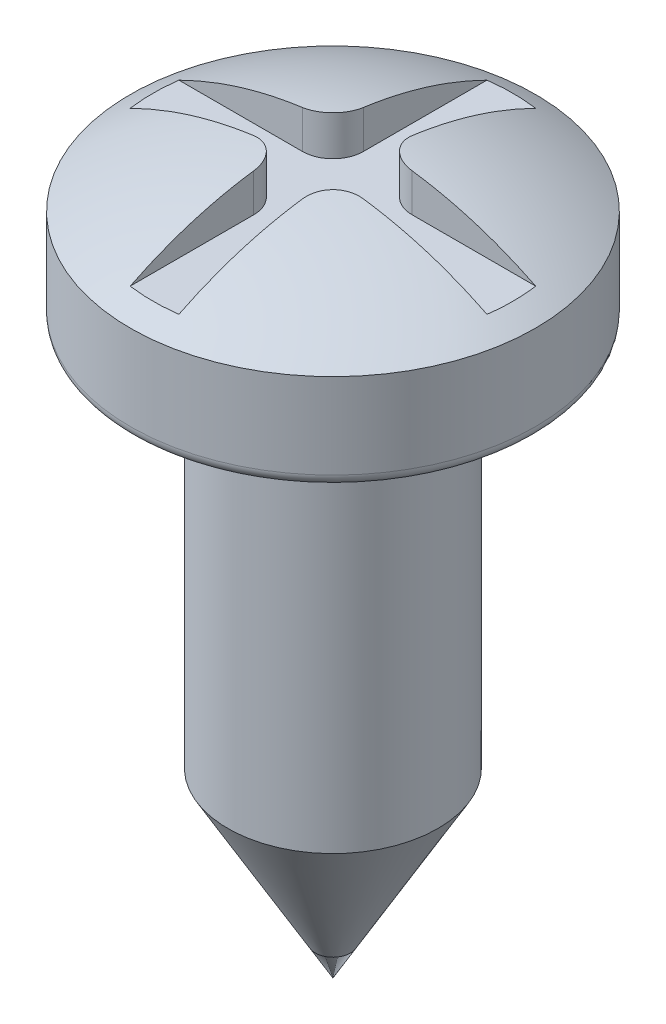
SolidWorks part; units mm, degrees
material "acero"
ref_plane "Alzado" through (0, 0, 0) normal (0, 0, 1) x (1, 0, 0)
ref_plane "Planta" through (0, 0, 0) normal (0, 1, 0) x (1, 0, 0)
ref_plane "Vista lateral" through (0, 0, 0) normal (1, 0, 0) x (0, 0, -1)
sketch "Croquis1" plane through (0, 0, 0) normal (0, 0, 1) x (1, 0, 0)
  line L0 (0, 0) -> (0, 11.8) construction
  line L1 (0, 0) -> (0, 11.8)
  line L2 (3.325, 9.5) -> (3.325, 10.9)
  line L3 (3.125, 9.3) -> (1.725, 9.3)
  line L4 (1.725, 9.3) -> (1.725, 2.9878)
  line L5 (1.725, 2.9878) -> (0, 0)
  line L6 (0, 11.8) -> (0, 14.3369) construction
  line L7 (0, 11.8) -> (-1.1321, 11.8) construction
  arc A0 (3.125, 9.3) -> (3.325, 9.5) centre (3.125, 9.5) ccw
  arc A1 (3.325, 10.9) -> (0, 11.8) centre (0, 5.208) ccw
  point P11 (3.325, 9.3)
  dimension "D7" = 0.2
  dimension "D1" = 1.6
  dimension "D2" = 30
  dimension "D3" = 2.5
  dimension "D4" = 3.45
  dimension "D5" = 6.65
  dimension "D9" = 9.3
revolve "Revolución1" add sketch "Croquis1" angle 360 about L0
sketch "Croquis2" plane through (0, 9.3, 0) normal (0, -1, 0) x (1, 0, 0)
  line L0 (0, 0) -> (0, 3.325) construction
  line L1 (-0.4, 3.2) -> (-0.4, 0.9)
  line L2 (-0.9, 0.4) -> (-3.2, 0.4)
  line L3 (-3.2, 0.4) -> (-3.2, -0.4)
  line L4 (-3.2, -0.4) -> (-0.9, -0.4)
  line L5 (-0.4, -0.9) -> (-0.4, -3.2)
  line L6 (-0.4, -3.2) -> (0.4, -3.2)
  line L7 (0.4, -3.2) -> (0.4, -0.9)
  line L8 (0.9, -0.4) -> (3.2, -0.4)
  line L9 (3.2, -0.4) -> (3.2, 0.4)
  line L10 (3.2, 0.4) -> (0.9, 0.4)
  line L11 (0.4, 0.9) -> (0.4, 3.2)
  line L12 (0.4, 3.2) -> (-0.4, 3.2)
  circle A0 centre (0, 0) radius 3.325 construction
  arc A1 (-0.4, -0.9) -> (-0.9, -0.4) centre (-0.9, -0.9) ccw
  arc A2 (0.4, -0.9) -> (0.9, -0.4) centre (0.9, -0.9) cw
  arc A3 (0.9, 0.4) -> (0.4, 0.9) centre (0.9, 0.9) cw
  arc A4 (-0.9, 0.4) -> (-0.4, 0.9) centre (-0.9, 0.9) ccw
  point P26 (-0.4, 0.4)
  dimension "D12" = 0.5
  dimension "D1" = 0.4
  dimension "D2" = 0.8
  dimension "D3" = 3.2
  dimension "D4" = 3.2
  dimension "D5" = 3.2
  dimension "D6" = 3.2
  dimension "D7" = 0.4
  dimension "D8" = 0.4
  dimension "D9" = 0.4
  dimension "D10" = 0.4
  dimension "D11" = 0.4
extrude "Cortar-Extruir1" cut sketch "Croquis2" against normal blind 3 from offset 1.8
